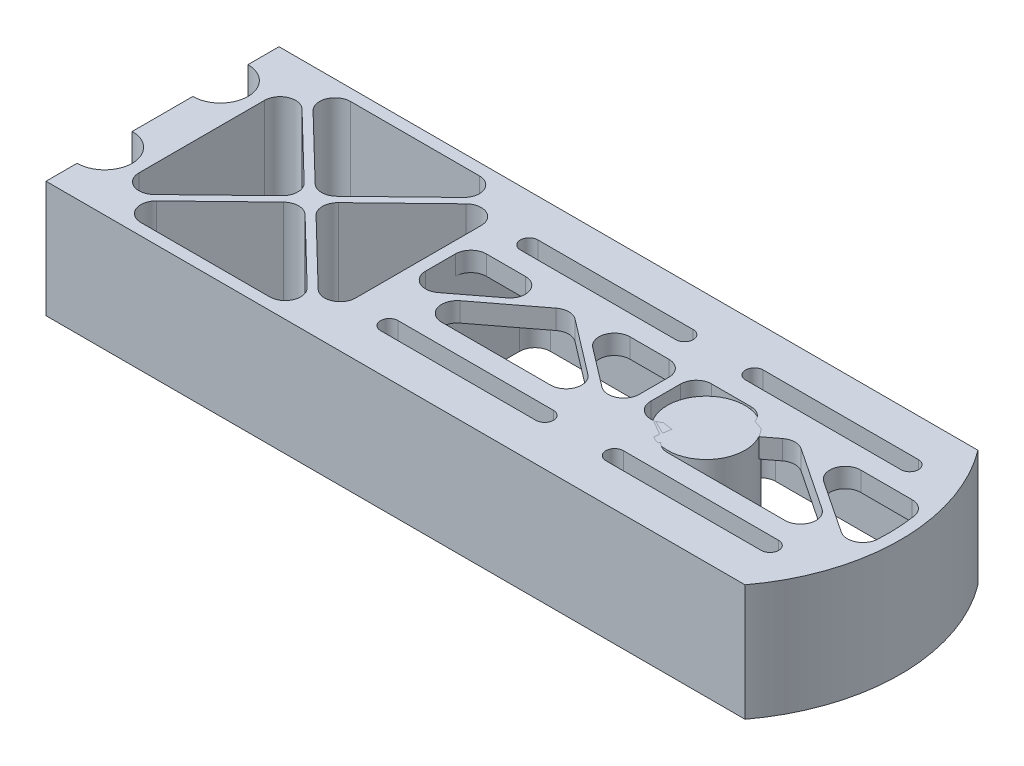
SolidWorks part; units mm, degrees
material "3.1355 (EN-AW 2024)"
ref_plane "Front" through (0, 0, 0) normal (0, 0, 1) x (1, 0, 0)
ref_plane "Top" through (0, 0, 0) normal (0, 1, 0) x (1, 0, 0)
ref_plane "Right" through (0, 0, 0) normal (1, 0, 0) x (0, 0, -1)
sketch "Эскиз1" plane through (0, 0, 0) normal (0, 1, 0) x (1, 0, 0)
  line L0 (0, 0) -> (0, 60) construction
  line L1 (0, 60) -> (180, 60)
  line L2 (190, 60) -> (190, 0) construction
  line L3 (190, 0) -> (180, 0) construction
  line L4 (0, 30) -> (140, 30) construction
  line L5 (0, 60) -> (0, 52)
  line L6 (0, 37.8) -> (0, 22.2)
  line L7 (0, 8) -> (0, 0)
  line L8 (140, 30) -> (190, 30) construction
  line L9 (180, 60) -> (190, 60) construction
  line L10 (180, 0) -> (0, 0)
  circle A0 centre (0, 44.9) radius 7.1 construction
  circle A1 centre (0, 15.1) radius 7.1 construction
  arc A2 (0, 52) -> (0, 37.8) centre (0, 44.9) cw
  arc A3 (0, 8) -> (0, 22.2) centre (0, 15.1) ccw
  arc A4 (180, 0) -> (180, 60) centre (140, 30) ccw
  point P11 (0, 52)
  point P12 (0, 37.8)
  dimension "D2" = 14.2
  dimension "D4" = 29.8
  dimension "D8" = 50
  dimension "D1" = 60
  dimension "D3" = 15.1
  dimension "D5" = 140
  dimension "D6" = 50
  dimension "D7" = 190
extrude "Бобышка-Вытянуть1" add sketch "Эскиз1" along normal blind 30
sketch "Эскиз2" plane through (0, 30, 0) normal (0, 1, 0) x (1, 0, 0)
  line L5 (3, 3) -> (178.4708, 3)
  line L6 (3, 3) -> (178.4708, 3)
  line L12 (3, 5.4558) -> (3, 3)
  line L15 (178.4708, 57) -> (3, 57)
  line L16 (3, 57) -> (3, 54.5442)
  line L17 (3, 35.2558) -> (3, 24.7442)
  line L18 (3, 5.4558) -> (3, 3)
  line L21 (178.4708, 57) -> (3, 57)
  line L22 (3, 57) -> (3, 54.5442)
  line L23 (3, 35.2558) -> (3, 24.7442)
  arc A3 (178.4708, 3) -> (178.4708, 57) centre (140, 30) ccw
  arc A4 (3, 35.2558) -> (3, 54.5442) centre (0, 44.9) ccw
  arc A5 (3, 5.4558) -> (3, 24.7442) centre (0, 15.1) ccw
  arc A6 (3, 35.2558) -> (3, 54.5442) centre (0, 44.9) ccw
  arc A7 (3, 5.4558) -> (3, 24.7442) centre (0, 15.1) ccw
  arc A8 (178.4708, 3) -> (178.4708, 57) centre (140, 30) ccw
  dimension "D1" = 3
extrude "Вырез-Вытянуть1" cut sketch "Эскиз2" against normal through all
sketch "Temp" plane through (0, 30, 0) normal (0, 1, 0) x (1, 0, 0)
  circle A0 centre (140, 30) radius 10
  dimension "D1" = 20
extrude "Бобышка-Вытянуть2" add sketch "Temp" against normal up to surface (30 mm away) separate body up to face at (49.7088, 0, -30)
sketch "Эскиз3" plane through (0, 30, 0) normal (0, 1, 0) x (1, 0, 0)
  line L0 (178.4708, 57) -> (3, 57) construction
  line L1 (174.4166, 48) -> (134.4166, 48) construction
  line L2 (174.4166, 43.5) -> (134.4166, 43.5)
  line L3 (174.4166, 52.5) -> (134.4166, 52.5)
  line L4 (174.4166, 48) -> (183.4166, 48) construction
  line L5 (125.4166, 57) -> (125.4166, 30) construction
  line L6 (0, 30) -> (140, 30) construction
  line L7 (76.4166, 48) -> (116.4166, 48) construction
  line L8 (76.4166, 43.5) -> (116.4166, 43.5)
  line L9 (76.4166, 52.5) -> (116.4166, 52.5)
  line L10 (187, 30) -> (125.4166, 30) construction
  line L11 (76.4166, 12) -> (116.4166, 12) construction
  line L12 (76.4166, 16.5) -> (116.4166, 16.5)
  line L13 (76.4166, 7.5) -> (116.4166, 7.5)
  line L14 (174.4166, 12) -> (134.4166, 12) construction
  line L15 (174.4166, 16.5) -> (134.4166, 16.5)
  line L16 (174.4166, 7.5) -> (134.4166, 7.5)
  line L17 (68.9166, 57) -> (68.9166, 40.5)
  line L18 (68.9166, 40.5) -> (185.8121, 40.5)
  line L19 (178.4708, 57) -> (68.9166, 57)
  line L20 (76.4166, 12) -> (116.4166, 12) construction
  line L21 (76.4166, 16.5) -> (116.4166, 16.5)
  line L22 (76.4166, 7.5) -> (116.4166, 7.5)
  line L23 (174.4166, 12) -> (134.4166, 12) construction
  line L24 (174.4166, 16.5) -> (134.4166, 16.5)
  line L25 (174.4166, 7.5) -> (134.4166, 7.5)
  line L26 (68.9166, 19.5) -> (185.8121, 19.5)
  line L27 (178.4708, 3) -> (68.9166, 3)
  line L28 (68.9166, 3) -> (68.9166, 19.5)
  arc A0 (174.4166, 43.5) -> (174.4166, 52.5) centre (174.4166, 48) ccw
  arc A1 (134.4166, 52.5) -> (134.4166, 43.5) centre (134.4166, 48) ccw
  arc A2 (178.4708, 3) -> (178.4708, 57) centre (140, 30) ccw construction
  arc A3 (76.4166, 43.5) -> (76.4166, 52.5) centre (76.4166, 48) cw
  arc A4 (116.4166, 52.5) -> (116.4166, 43.5) centre (116.4166, 48) cw
  arc A5 (76.4166, 16.5) -> (76.4166, 7.5) centre (76.4166, 12) ccw
  arc A6 (116.4166, 7.5) -> (116.4166, 16.5) centre (116.4166, 12) ccw
  arc A7 (174.4166, 16.5) -> (174.4166, 7.5) centre (174.4166, 12) cw
  arc A8 (134.4166, 7.5) -> (134.4166, 16.5) centre (134.4166, 12) cw
  arc A9 (185.8121, 40.5) -> (178.4708, 57) centre (140, 30) ccw
  arc A10 (76.4166, 16.5) -> (76.4166, 7.5) centre (76.4166, 12) ccw
  arc A11 (116.4166, 7.5) -> (116.4166, 16.5) centre (116.4166, 12) ccw
  arc A12 (174.4166, 16.5) -> (174.4166, 7.5) centre (174.4166, 12) cw
  arc A13 (134.4166, 7.5) -> (134.4166, 16.5) centre (134.4166, 12) cw
  arc A14 (185.8121, 19.5) -> (178.4708, 3) centre (140, 30) cw
  point P1 (154.4166, 48)
  point P20 (96.4166, 48)
  point P28 (96.4166, 12)
  point P35 (154.4166, 12)
  arc M3 (178.4708, 57) -> (178.4708, 3) centre (140, 30) cw
  line M4 (178.4708, 3) -> (3, 3)
  line M10 (3, 57) -> (178.4708, 57)
  dimension "D1" = 4.5
  dimension "D6" = 3
  dimension "D2" = 40
  dimension "D3" = 9
  dimension "D4" = 9
  dimension "D5" = 9
  dimension "D7" = 7.5
extrude "Бобышка-Вытянуть3" add sketch "Эскиз3" against normal blind 5 contours L17 L18 A1 L3 A0 L2 L9 A4 L8 A3 M3 M10 | L28 L26 A6 L13 A5 L12 L16 A8 L15 A7 M4 M3
sketch "Эскиз4" plane through (0, 30, 0) normal (0, 1, 0) x (1, 0, 0)
  line L0 (3, 57) -> (3, 54.5442) construction
  line L1 (3, 35.2558) -> (3, 24.7442) construction
  line L2 (3, 5.4558) -> (3, 3) construction
  line L3 (3, 3) -> (68.9166, 3) construction
  line L4 (68.9166, 57) -> (3, 57) construction
  line L5 (3, 57) -> (3, 54.5442)
  line L6 (3, 35.2558) -> (3, 24.7442)
  line L7 (3, 5.4558) -> (3, 3)
  line L8 (3, 3) -> (10.1, 3)
  line L9 (10.1, 57) -> (3, 57)
  line L10 (10.1, 57) -> (10.1, 3)
  arc A0 (3, 35.2558) -> (3, 54.5442) centre (0, 44.9) ccw construction
  arc A1 (3, 5.4558) -> (3, 24.7442) centre (0, 15.1) ccw construction
  arc A2 (3, 35.2558) -> (3, 54.5442) centre (0, 44.9) ccw
  arc A3 (3, 5.4558) -> (3, 24.7442) centre (0, 15.1) ccw
  line M4 (68.9166, 3) -> (3, 3)
  line M5 (3, 3) -> (3, 5.4558)
  arc M6 (3, 5.4558) -> (3, 24.7442) centre (0, 15.1) ccw
  line M7 (3, 24.7442) -> (3, 35.2558)
  arc M8 (3, 35.2558) -> (3, 54.5442) centre (0, 44.9) ccw
  line M9 (3, 54.5442) -> (3, 57)
  line M10 (3, 57) -> (68.9166, 57)
extrude "Бобышка-Вытянуть4" add sketch "Эскиз4" against normal through all contours L10 M10 M9 M8 | L10 M8 M7 M6 | L10 M6 M5 M4
sketch "Эскиз6" plane through (0, 30, 0) normal (0, 1, 0) x (1, 0, 0)
  line L0 (65.9166, 57) -> (65.9166, 3)
  line L1 (68.9166, 57) -> (10.1, 57) construction
  line L2 (10.1, 3) -> (68.9166, 3) construction
  line L3 (68.9166, 57) -> (68.9166, 40.5) construction
  line L4 (65.9166, 3) -> (68.9166, 3)
  line L5 (68.9166, 3) -> (68.9166, 57)
  line L6 (68.9166, 57) -> (65.9166, 57)
  dimension "D1" = 3
extrude "Бобышка-Вытянуть5" add sketch "Эскиз6" against normal through all
sketch "Эскиз7" plane through (0, 30, 0) normal (0, 1, 0) x (1, 0, 0)
  line L0 (10.1, 3) -> (65.9166, 57) construction
  line L1 (10.1, 57) -> (65.9166, 3) construction
  line L2 (10.1, 55.6086) -> (36.5701, 30)
  line L3 (11.5382, 3) -> (38.0083, 28.6086)
  line L4 (11.5382, 57) -> (38.0083, 31.3914)
  line L5 (10.1, 4.3914) -> (36.5701, 30)
  line L6 (65.9166, 57) -> (10.1, 57) construction
  line L7 (10.1, 57) -> (10.1, 3) construction
  line L8 (10.1, 3) -> (65.9166, 3) construction
  line L9 (65.9166, 57) -> (65.9166, 3) construction
  line L10 (65.9166, 57) -> (64.4784, 57)
  line L11 (10.1, 57) -> (10.1, 55.6086)
  line L12 (10.1, 3) -> (11.5382, 3)
  line L13 (65.9166, 57) -> (65.9166, 55.6086)
  line L14 (11.5382, 57) -> (10.1, 57)
  line L15 (10.7953, 57.7187) -> (66.6119, 3.7187) construction
  line L16 (9.4047, 56.2813) -> (65.2213, 2.2813) construction
  line L17 (65.9166, 4.3914) -> (65.9166, 3)
  line L18 (9.4047, 3.7187) -> (65.2213, 57.7187) construction
  line L19 (10.7953, 2.2813) -> (66.6119, 56.2813) construction
  line L20 (64.4784, 3) -> (65.9166, 3)
  line L21 (10.1, 4.3914) -> (10.1, 3)
  line L22 (39.4465, 30) -> (65.9166, 55.6086)
  line L23 (39.4465, 30) -> (65.9166, 4.3914)
  line L24 (38.0083, 31.3914) -> (64.4784, 57)
  line L25 (38.0083, 28.6086) -> (64.4784, 3)
  dimension "D1" = 1
  dimension "D2" = 1
extrude "Бобышка-Вытянуть6" add sketch "Эскиз7" against normal through all
sketch "Эскиз9" plane through (0, 25, 0) normal (0, -1, 0) x (1, 0, 0)
  line L0 (120.9166, -12) -> (129.9166, -12) construction
  line L1 (125.4166, -3) -> (125.4166, -57) construction
  line L2 (68.9166, -57) -> (178.4708, -57) construction
  line L3 (123.9166, -3) -> (123.9166, -57)
  line L4 (101.5292, -3) -> (68.9166, -3) construction
  line L5 (126.9166, -3) -> (126.9166, -57)
  line L6 (123.9166, -3) -> (126.9166, -3)
  line L7 (123.9166, -57) -> (126.9166, -57)
  arc A0 (116.4166, -16.5) -> (116.4166, -7.5) centre (116.4166, -12) ccw construction
  arc A1 (134.4166, -16.5) -> (134.4166, -7.5) centre (134.4166, -12) ccw construction
  point P8 (125.4166, -12)
  dimension "D1" = 1.5
  dimension "D2" = 1.5
extrude "Бобышка-Вытянуть8" add sketch "Эскиз9" along normal through all and the other way through all
sketch "Эскиз8" plane through (0, 30, 0) normal (0, 1, 0) x (1, 0, 0)
  line L0 (96.4166, 43.5) -> (96.4166, 16.5) construction
  line L1 (76.4166, 43.5) -> (116.4166, 43.5) construction
  line L2 (76.4166, 16.5) -> (116.4166, 16.5) construction
  line L3 (154.4166, 43.5) -> (154.4166, 16.5) construction
  line L4 (174.4166, 43.5) -> (134.4166, 43.5) construction
  line L5 (174.4166, 16.5) -> (134.4166, 16.5) construction
  line L6 (68.9166, 19.5) -> (96.4166, 40.5) construction
  line L7 (116.4166, 48) -> (134.4166, 48) construction
  line L8 (125.4166, 48) -> (125.4166, 19.5) construction
  line L9 (68.9166, 40.5) -> (123.9166, 40.5) construction
  line L10 (96.4166, 40.5) -> (123.9166, 19.5) construction
  line L11 (126.9166, 19.5) -> (154.4401, 40.4052) construction
  line L12 (154.4401, 40.4052) -> (185.8121, 19.5) construction
  line L13 (70.5643, 19.5) -> (96.4166, 39.2418)
  line L14 (96.4166, 39.2418) -> (122.2689, 19.5)
  line L15 (128.5699, 19.5) -> (154.478, 39.1782)
  line L16 (154.478, 39.1782) -> (184.0088, 19.5)
  line L17 (68.9166, 20.7582) -> (94.7689, 40.5)
  line L18 (98.0643, 40.5) -> (123.9166, 20.7582)
  line L19 (126.9166, 20.7557) -> (152.9116, 40.5)
  line L20 (122.2689, 19.5) -> (123.9166, 19.5)
  line L22 (94.7689, 40.5) -> (98.0643, 40.5)
  line L23 (68.9166, 19.5) -> (68.9166, 40.5) construction
  line L24 (68.9166, 19.5) -> (123.9166, 19.5) construction
  line L25 (123.9166, 19.5) -> (123.9166, 40.5) construction
  line L26 (126.9166, 40.5) -> (126.9166, 19.5) construction
  line L27 (126.9166, 40.5) -> (185.8121, 40.5) construction
  line L28 (126.9166, 19.5) -> (185.8121, 19.5) construction
  line L29 (68.9166, 19.5) -> (68.9166, 20.7582)
  line L30 (68.9166, 19.5) -> (70.5643, 19.5)
  line L31 (123.9166, 19.5) -> (123.9166, 20.7582)
  line L32 (126.9166, 20.7557) -> (126.9166, 19.5)
  line L33 (152.9116, 40.5) -> (156.1011, 40.5)
  line L34 (126.9166, 19.5) -> (128.5699, 19.5)
  line L35 (184.0088, 19.5) -> (185.8121, 19.5)
  line L36 (154.4021, 41.6321) -> (186.3666, 20.3322) construction
  line L37 (154.478, 39.1782) -> (185.2576, 18.6678) construction
  line L38 (156.1011, 40.5) -> (186.0401, 20.5497)
  line L39 (127.5214, 18.7037) -> (154.478, 39.1782) construction
  line L40 (126.3117, 20.2963) -> (154.4021, 41.6321) construction
  line L42 (96.4166, 41.7582) -> (124.5235, 20.2948) construction
  line L43 (68.3097, 20.2948) -> (96.4166, 41.7582) construction
  line L44 (69.5235, 18.7052) -> (96.4166, 39.2418) construction
  line L45 (96.4166, 39.2418) -> (123.3097, 18.7052) construction
  arc A1 (185.8121, 19.5) -> (185.8121, 40.5) centre (140, 30) ccw construction
  arc A2 (185.8121, 19.5) -> (186.0401, 20.5497) centre (140, 30) ccw
  point P26 (69.5235, 18.7052)
  point P27 (96.4324, 39.2539)
  point P28 (125.4324, 18.2539)
  point P30 (185.2357, 18.6828)
  point P31 (68.3097, 20.2948)
  point P32 (96.4007, 41.7461)
  point P33 (125.4007, 20.7461)
  point P34 (154.3931, 42.8858)
  point P35 (186.3885, 20.3172)
  point P49 (154.4166, 40.5)
  dimension "D1" = 1
  dimension "D2" = 1
extrude "Бобышка-Вытянуть7" add sketch "Эскиз8" against normal up to surface (5 mm away) up to face at (96.4166, 25, -12)
fillet "Скругление1" radius 4 12 edges at (11.5382, 15, -57) (38.0083, 15, -31.3914) (64.4784, 15, -57) (65.9166, 15, -55.6086) (39.4465, 15, -30) (65.9166, 15, -4.3914) (11.5382, 15, -3) (64.4784, 15, -3) (38.0083, 15, -28.6086) (10.1, 15, -4.3914) (36.5701, 15, -30) (10.1, 15, -55.6086)
fillet "Скругление2" radius 4 8 edges at (178.4708, 12.5, -57) (178.4708, 12.5, -3) (126.9166, 12.5, -3) (126.9166, 12.5, -57) (123.9166, 12.5, -3) (68.9166, 12.5, -3) (68.9166, 12.5, -57) (123.9166, 12.5, -57)
fillet "Скругление3" radius 4 18 edges at (98.0643, 27.5, -40.5) (123.9166, 27.5, -40.5) (123.9166, 27.5, -20.7582) (122.2689, 27.5, -19.5) (96.4166, 27.5, -39.2418) (70.5643, 27.5, -19.5) (94.7689, 27.5, -40.5) (68.9166, 27.5, -40.5) (68.9166, 27.5, -20.7582) (185.8121, 27.5, -40.5) (156.1011, 27.5, -40.5) (186.0401, 27.5, -20.5497) (184.0088, 27.5, -19.5) (154.478, 27.5, -39.1782) (128.5699, 27.5, -19.5) (126.9166, 27.5, -20.7557) (152.9116, 27.5, -40.5) (126.9166, 27.5, -40.5)
sketch "Эскиз10" plane through (0, 30, 0) normal (0, 1, 0) x (1, 0, 0)
  line L90 (76.4166, 52.5) -> (116.4166, 52.5) construction
  line L91 (76.4166, 43.5) -> (116.4166, 43.5) construction
  line L92 (116.4166, 50.25) -> (76.4166, 50.25)
  line L93 (76.4166, 45.75) -> (116.4166, 45.75)
  line L94 (116.4166, 50.25) -> (76.4166, 50.25)
  line L95 (76.4166, 45.75) -> (116.4166, 45.75)
  line L96 (76.4166, 52.5) -> (116.4166, 52.5)
  line L97 (76.4166, 43.5) -> (116.4166, 43.5)
  line L98 (174.4166, 52.5) -> (134.4166, 52.5) construction
  line L99 (174.4166, 43.5) -> (134.4166, 43.5) construction
  line L100 (174.4166, 52.5) -> (134.4166, 52.5)
  line L101 (174.4166, 43.5) -> (134.4166, 43.5)
  line L102 (76.4166, 16.5) -> (116.4166, 16.5) construction
  line L103 (76.4166, 7.5) -> (116.4166, 7.5) construction
  line L104 (76.4166, 16.5) -> (116.4166, 16.5)
  line L105 (76.4166, 7.5) -> (116.4166, 7.5)
  line L106 (174.4166, 16.5) -> (134.4166, 16.5) construction
  line L107 (174.4166, 7.5) -> (134.4166, 7.5) construction
  line L108 (174.4166, 16.5) -> (134.4166, 16.5)
  line L109 (174.4166, 7.5) -> (134.4166, 7.5)
  line L110 (174.4166, 45.75) -> (134.4166, 45.75)
  line L111 (174.4166, 50.25) -> (134.4166, 50.25)
  line L112 (174.4166, 14.25) -> (134.4166, 14.25)
  line L113 (174.4166, 9.75) -> (134.4166, 9.75)
  line L114 (76.4166, 9.75) -> (116.4166, 9.75)
  line L115 (76.4166, 14.25) -> (116.4166, 14.25)
  arc A90 (76.4166, 52.5) -> (76.4166, 43.5) centre (76.4166, 48) ccw construction
  arc A91 (116.4166, 43.5) -> (116.4166, 52.5) centre (116.4166, 48) ccw construction
  arc A92 (76.4166, 50.25) -> (76.4166, 45.75) centre (76.4166, 48) ccw
  arc A93 (116.4166, 45.75) -> (116.4166, 50.25) centre (116.4166, 48) ccw
  arc A94 (76.4166, 50.25) -> (76.4166, 45.75) centre (76.4166, 48) ccw
  arc A95 (116.4166, 45.75) -> (116.4166, 50.25) centre (116.4166, 48) ccw
  arc A96 (76.4166, 52.5) -> (76.4166, 43.5) centre (76.4166, 48) ccw
  arc A97 (116.4166, 43.5) -> (116.4166, 52.5) centre (116.4166, 48) ccw
  arc A98 (134.4166, 52.5) -> (134.4166, 43.5) centre (134.4166, 48) ccw construction
  arc A99 (174.4166, 43.5) -> (174.4166, 52.5) centre (174.4166, 48) ccw construction
  arc A100 (134.4166, 52.5) -> (134.4166, 43.5) centre (134.4166, 48) ccw
  arc A101 (174.4166, 43.5) -> (174.4166, 52.5) centre (174.4166, 48) ccw
  arc A102 (116.4166, 7.5) -> (116.4166, 16.5) centre (116.4166, 12) ccw construction
  arc A103 (76.4166, 16.5) -> (76.4166, 7.5) centre (76.4166, 12) ccw construction
  arc A104 (116.4166, 7.5) -> (116.4166, 16.5) centre (116.4166, 12) ccw
  arc A105 (76.4166, 16.5) -> (76.4166, 7.5) centre (76.4166, 12) ccw
  arc A106 (134.4166, 16.5) -> (134.4166, 7.5) centre (134.4166, 12) ccw construction
  arc A107 (174.4166, 7.5) -> (174.4166, 16.5) centre (174.4166, 12) ccw construction
  arc A108 (134.4166, 16.5) -> (134.4166, 7.5) centre (134.4166, 12) ccw
  arc A109 (174.4166, 7.5) -> (174.4166, 16.5) centre (174.4166, 12) ccw
  arc A110 (134.4166, 50.25) -> (134.4166, 45.75) centre (134.4166, 48) ccw
  arc A111 (174.4166, 45.75) -> (174.4166, 50.25) centre (174.4166, 48) ccw
  arc A112 (134.4166, 14.25) -> (134.4166, 9.75) centre (134.4166, 12) ccw
  arc A113 (174.4166, 9.75) -> (174.4166, 14.25) centre (174.4166, 12) ccw
  arc A114 (76.4166, 14.25) -> (76.4166, 9.75) centre (76.4166, 12) ccw
  arc A115 (116.4166, 9.75) -> (116.4166, 14.25) centre (116.4166, 12) ccw
  dimension "D1" = 2.25
  dimension "D2" = 2.25
  dimension "D3" = 2.25
  dimension "D4" = 2.25
extrude "Бобышка-Вытянуть9" add sketch "Эскиз10" against normal up to surface (5 mm away) up to face at (155.2427, 25, -27.7696)
equation "\"D3@Эскиз1\"=8+\"D2@Эскиз1\"/2"
equation "\"D7@Эскиз3\"=\"D1@Эскиз3\"+3"
